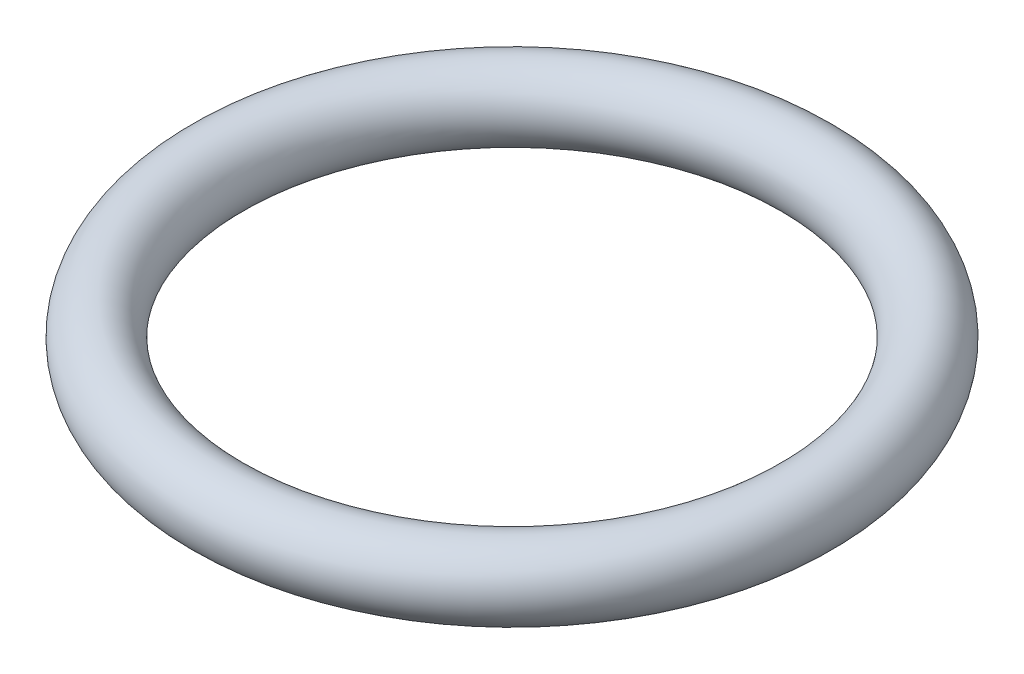
SolidWorks part; units mm, degrees
material "Silicon Rubber"
ref_plane "Front Plane" through (0, 0, 0) normal (0, 0, 1) x (1, 0, 0)
ref_plane "Top Plane" through (0, 0, 0) normal (0, 1, 0) x (1, 0, 0)
ref_plane "Right Plane" through (0, 0, 0) normal (1, 0, 0) x (0, 0, -1)
sketch "Sketch1" plane through (0, 0, 0) normal (0, 0, 1) x (1, 0, 0)
  line L0 (0, 3.4333) -> (0, -3.908) construction
  line L1 (-12.8224, 0) -> (6.3223, 0) construction
  circle A0 centre (-8.25, 0) radius 1
  dimension "D1" = 2
  dimension "D2" = 8.25
revolve "Revolve1" add sketch "Sketch1" angle 360 about L0
